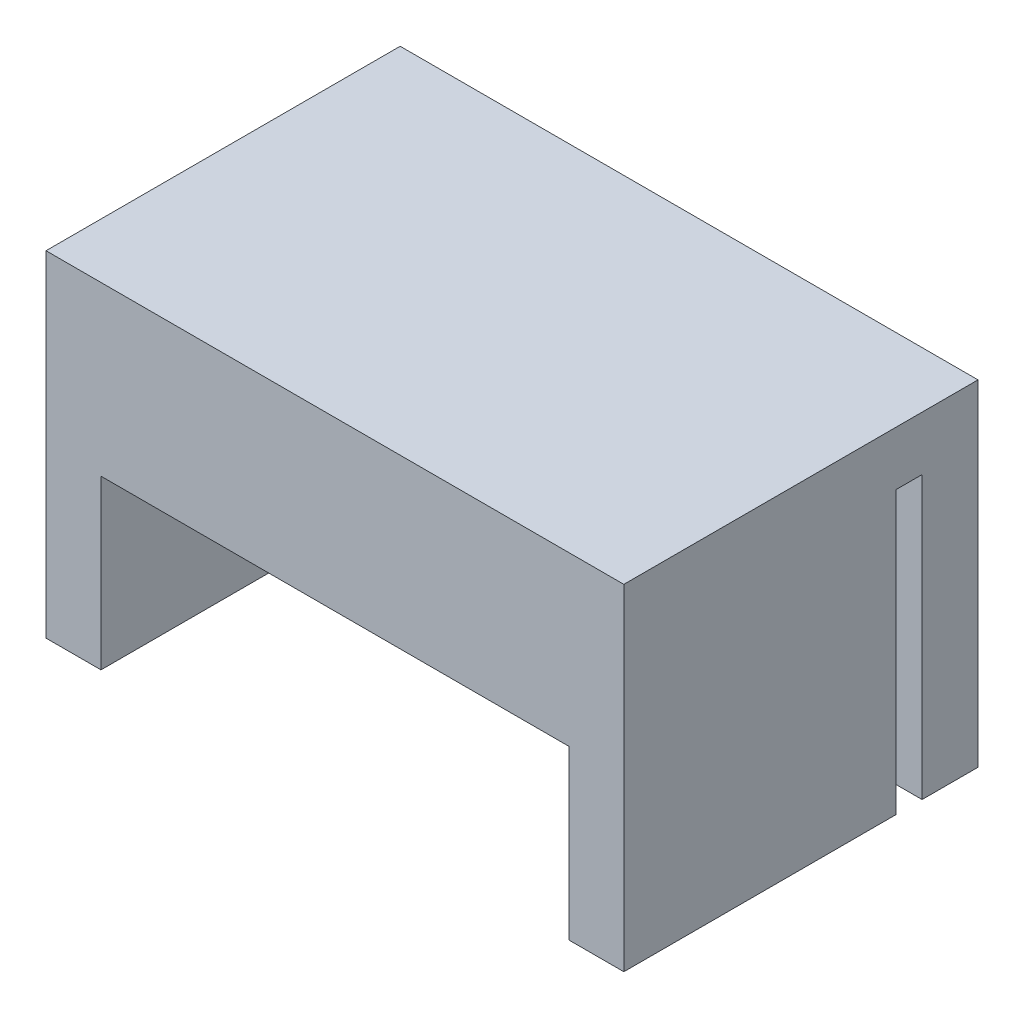
SolidWorks part; units mm, degrees
ref_plane "Alzado" through (0, 0, 0) normal (0, 0, 1) x (1, 0, 0)
ref_plane "Planta" through (0, 0, 0) normal (0, 1, 0) x (1, 0, 0)
ref_plane "Vista lateral" through (0, 0, 0) normal (1, 0, 0) x (0, 0, -1)
sketch "Croquis1" plane through (0, 0, 0) normal (0, 0, 1) x (1, 0, 0)
  line L1 (-15.5, -9) -> (15.5, -9)
  line L2 (-15.5, -9) -> (-15.5, 9)
  line L3 (-15.5, 9) -> (15.5, 9)
  line L4 (15.5, -9) -> (15.5, 9)
  line L5 (-15.5, -9) -> (15.5, 9) construction
  line L6 (-15.5, 9) -> (15.5, -9) construction
  point P0 (0, 0)
  dimension "D1" = 31
  dimension "D2" = 18
extrude "Saliente-Extruir1" add sketch "Croquis1" along normal blind 19
sketch "Croquis3" plane through (0, 0, 19) normal (0, 0, 1) x (1, 0, 0)
  line L0 (-15.5, -9) -> (15.5, -9) construction
  line L1 (-12.55, -9) -> (12.55, -9)
  line L2 (-12.55, -9) -> (-12.55, 0)
  line L3 (-12.55, 0) -> (12.55, 0)
  line L4 (12.55, -9) -> (12.55, 0)
  line L5 (0, -9) -> (0, 0) construction
  dimension "D1" = 25.1
  dimension "D2" = 9
extrude "Cortar-Extruir1" cut sketch "Croquis3" against normal blind 16
sketch "Croquis4" plane through (0, -9, 0) normal (0, -1, 0) x (1, 0, 0)
  line L0 (-15.5, 19) -> (-15.5, 0) construction
  line L1 (-15.5, 4.4) -> (15.5, 4.4)
  line L2 (-15.5, 4.4) -> (-15.5, 3)
  line L3 (-15.5, 3) -> (15.5, 3)
  line L4 (15.5, 4.4) -> (15.5, 3)
  line L5 (15.5, 19) -> (15.5, 0) construction
  line L6 (-12.55, 3) -> (12.55, 3) construction
  dimension "D1" = 1.4
extrude "Cortar-Extruir2" cut sketch "Croquis4" against normal blind 15.1
sketch "Croquis5" plane through (0, 0, 0) normal (0, 0, -1) x (-1, 0, 0)
  circle A0 centre (-7.5, -4.35) radius 1.5
  circle A1 centre (7.5, -4.35) radius 1.5
  circle A4 centre (-7.5, -4.35) radius 2.675 construction
  circle A5 centre (7.5, -4.35) radius 2.675 construction
  dimension "D1" = 3
extrude "Cortar-Extruir3" cut sketch "Croquis5" against normal through all
